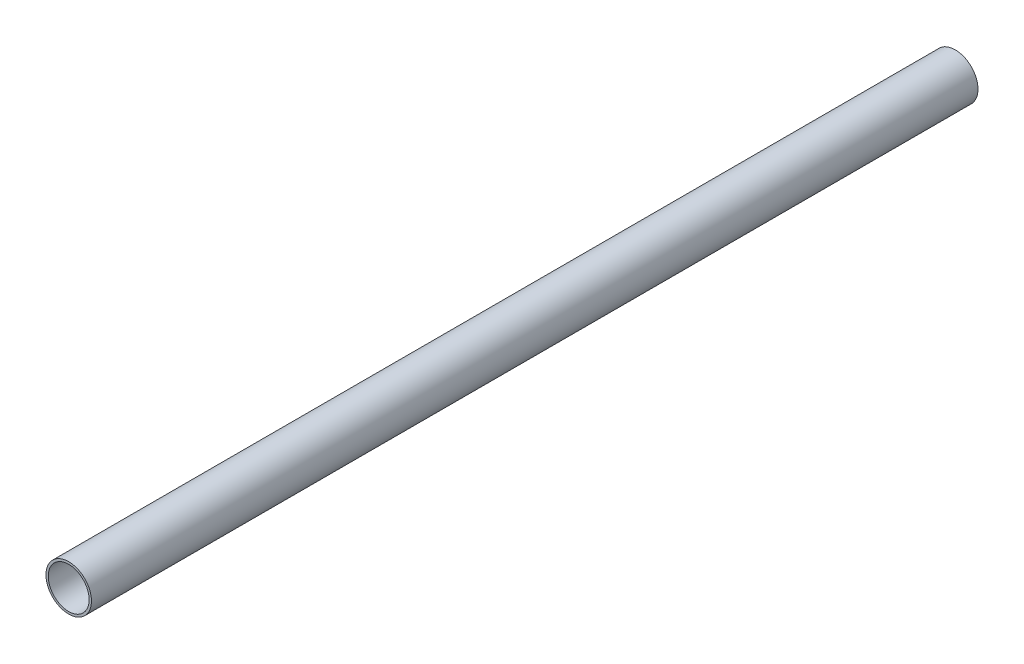
SolidWorks part; units mm, degrees
material "carbon fiber"
ref_plane "Front Plane" through (0, 0, 0) normal (0, 0, 1) x (1, 0, 0)
ref_plane "Top Plane" through (0, 0, 0) normal (0, 1, 0) x (1, 0, 0)
ref_plane "Right Plane" through (0, 0, 0) normal (1, 0, 0) x (0, 0, -1)
sketch "Эскиз1" plane through (0, 0, 0) normal (0, 0, 1) x (1, 0, 0)
  circle A0 centre (0, 0) radius 5
  circle A1 centre (0, 0) radius 4.5
  dimension "D1" = 10
  dimension "D2" = 0.5
extrude "Бобышка-Вытянуть1" add sketch "Эскиз1" along normal mid plane 195
